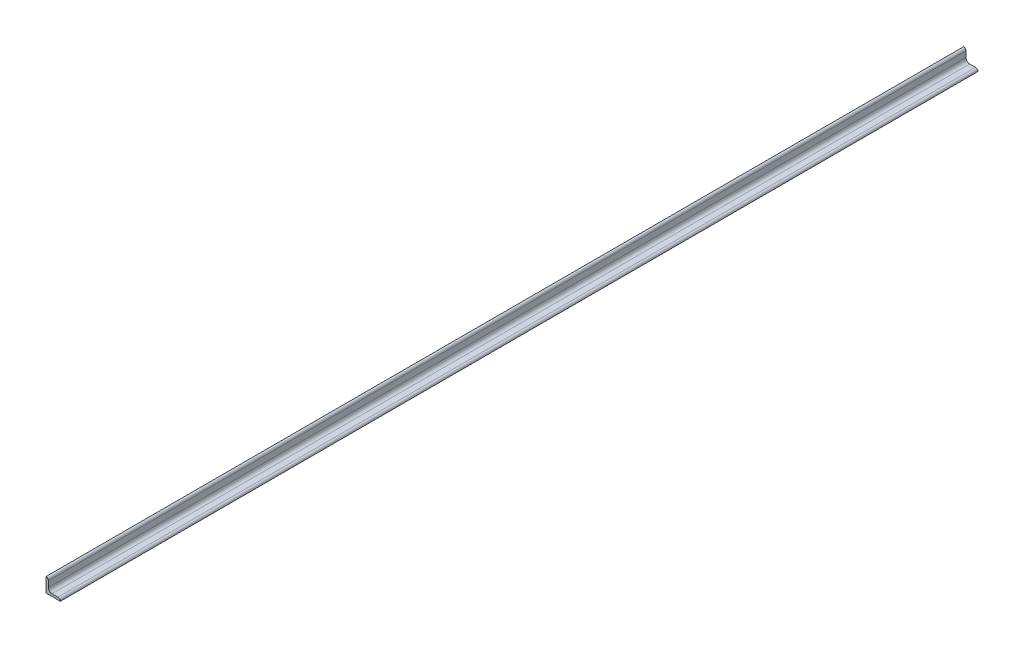
SolidWorks part; units mm, degrees
ref_plane "Front Plane" through (0, 0, 0) normal (0, 0, 1) x (1, 0, 0)
ref_plane "Top Plane" through (0, 0, 0) normal (0, 1, 0) x (1, 0, 0)
ref_plane "Right Plane" through (0, 0, 0) normal (1, 0, 0) x (0, 0, -1)
sketch "Sketch1" plane through (0, 0, 0) normal (0, 0, 1) x (1, 0, 0)
  line L0 (0, 0) -> (0, 19.05)
  line L1 (0, 19.05) -> (0.0051, 19.05)
  line L2 (3.175, 15.8801) -> (3.175, 7.9375)
  line L3 (7.9375, 3.175) -> (15.8801, 3.175)
  line L4 (19.05, 0.0051) -> (19.05, 0)
  line L5 (19.05, 0) -> (0, 0)
  arc A0 (19.05, 0.0051) -> (15.8801, 3.175) centre (15.8801, 0.0051) ccw
  arc A1 (0.0051, 19.05) -> (3.175, 15.8801) centre (0.0051, 15.8801) cw
  arc A2 (7.9375, 3.175) -> (3.175, 7.9375) centre (7.9375, 7.9375) cw
  circle A3 centre (0, 0) radius 3.175 construction
  dimension "D2" = 0.0051
  dimension "Radius_1" = 4.7625
  dimension "Radius_2" = 3.175
  dimension "D1" = 3.175
  dimension "V_leg" = 19.05
  dimension "H_leg" = 19.05
  dimension "Thickness" = 3.175
  dimension "Flat_wid" = 0.0051
extrude "Boss-Extrude1" add sketch "Sketch1" along normal mid plane 1219.2
